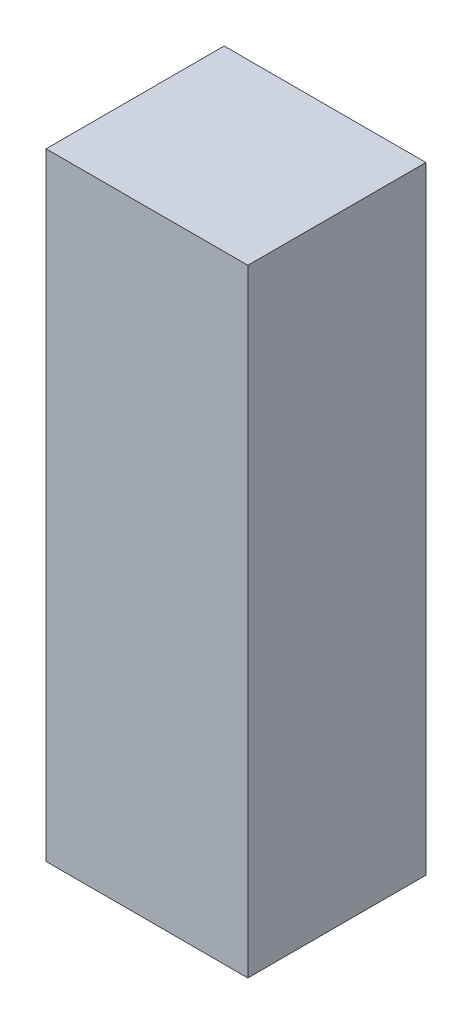
SolidWorks part; units mm, degrees
ref_plane "Front Plane" through (0, 0, 0) normal (0, 0, 1) x (1, 0, 0)
ref_plane "Top Plane" through (0, 0, 0) normal (0, 1, 0) x (1, 0, 0)
ref_plane "Right Plane" through (0, 0, 0) normal (1, 0, 0) x (0, 0, -1)
sketch "Sketch1" plane through (0, 0, 0) normal (0, 1, 0) x (1, 0, 0)
  line L1 (17, -15) -> (-17, -15)
  line L2 (17, -15) -> (17, 15)
  line L3 (17, 15) -> (-17, 15)
  line L4 (-17, -15) -> (-17, 15)
  line L5 (17, -15) -> (-17, 15) construction
  line L6 (17, 15) -> (-17, -15) construction
  point P0 (0, 0)
  dimension "D1" = 30
  dimension "D2" = 34
extrude "Boss-Extrude1" add sketch "Sketch1" along normal blind 104
